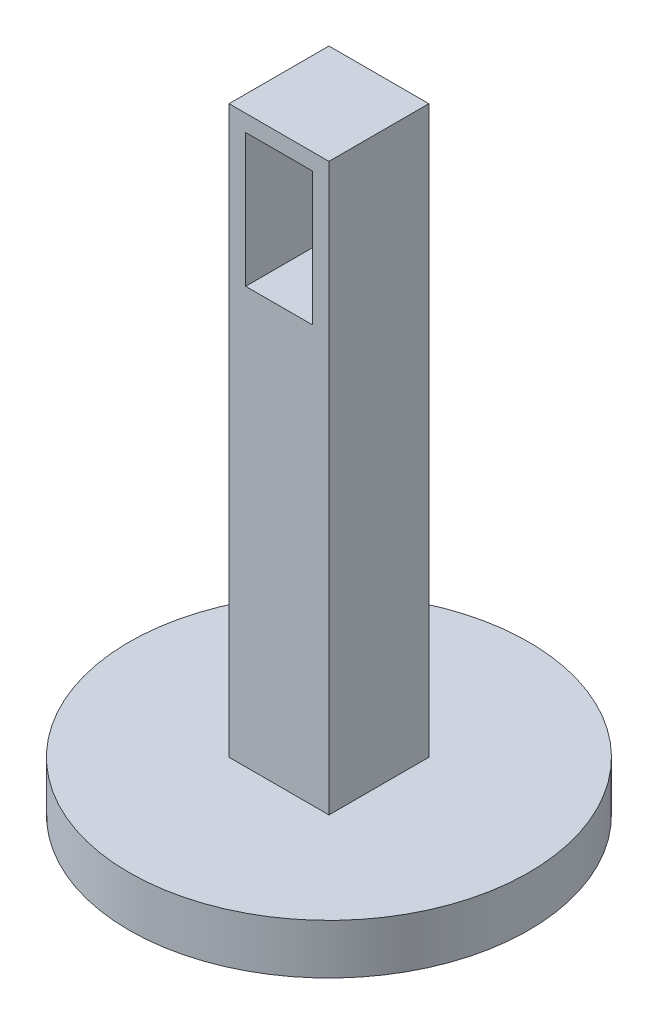
SolidWorks part; units mm, degrees
ref_plane "Front Plane" through (0, 0, 0) normal (0, 0, 1) x (1, 0, 0)
ref_plane "Top Plane" through (0, 0, 0) normal (0, 1, 0) x (1, 0, 0)
ref_plane "Right Plane" through (0, 0, 0) normal (1, 0, 0) x (0, 0, -1)
sketch "Sketch1" plane through (0, 0, 0) normal (0, 1, 0) x (1, 0, 0)
  circle A0 centre (0, 0) radius 60
  dimension "D1" = 120
extrude "Boss-Extrude1" add sketch "Sketch1" along normal blind 15 contours A0
sketch "Sketch3" plane through (0, 15, 0) normal (0, 1, 0) x (1, 0, 0)
  line L1 (-15, 15) -> (15, 15)
  line L2 (-15, 15) -> (-15, -15)
  line L3 (-15, -15) -> (15, -15)
  line L4 (15, 15) -> (15, -15)
  line L5 (-15, 15) -> (15, -15) construction
  line L6 (-15, -15) -> (15, 15) construction
  point P0 (0, 0)
  dimension "D1" = 30
  dimension "D2" = 30
extrude "Boss-Extrude2" add sketch "Sketch3" along normal blind 170
sketch "Sketch4" plane through (0, 0, 15) normal (0, 0, 1) x (1, 0, 0)
  line L0 (15, 185) -> (15, 15) construction
  line L1 (-15, 185) -> (15, 185)
  line L2 (-15, 185) -> (-15, 135)
  line L3 (-15, 135) -> (15, 135)
  line L4 (15, 185) -> (15, 135)
  line L9 (-10, 180) -> (10, 180)
  line L10 (10, 180) -> (10, 140)
  line L11 (-10, 140) -> (10, 140)
  line L12 (-10, 180) -> (-10, 140)
  dimension "D1" = 50
  dimension "D2" = 5
extrude "Cut-Extrude1" cut sketch "Sketch4" against normal blind 20 contours L9 L10 L11 L12
